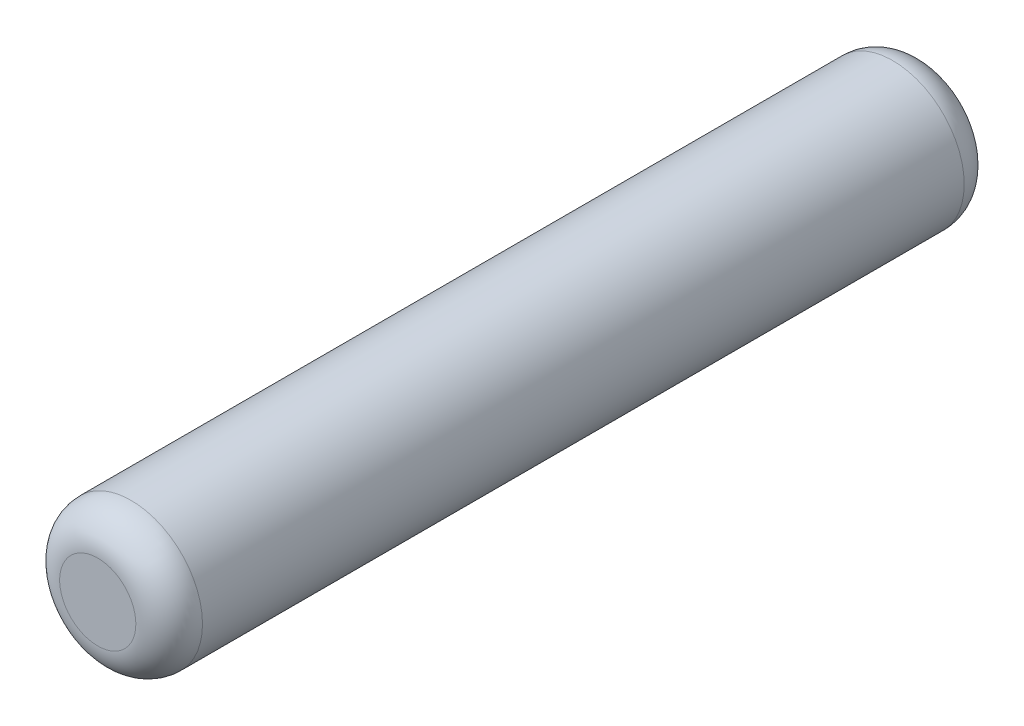
SolidWorks part; units mm, degrees
ref_plane "Front" through (0, 0, 0) normal (0, 0, 1) x (1, 0, 0)
ref_plane "Top" through (0, 0, 0) normal (0, 1, 0) x (1, 0, 0)
ref_plane "Right" through (0, 0, 0) normal (1, 0, 0) x (0, 0, -1)
sketch "Sketch1" plane through (0, 0, 0) normal (0, 0, 1) x (1, 0, 0)
  circle A0 centre (0, 0) radius 0.75
  dimension "D1" = 1.5
extrude "Boss-Extrude1" add sketch "Sketch1" along normal mid plane 8.7
fillet "Fillet1" radius 0.35 2 edges at (0.75, 0, -4.35) (0.75, 0, 4.35)
